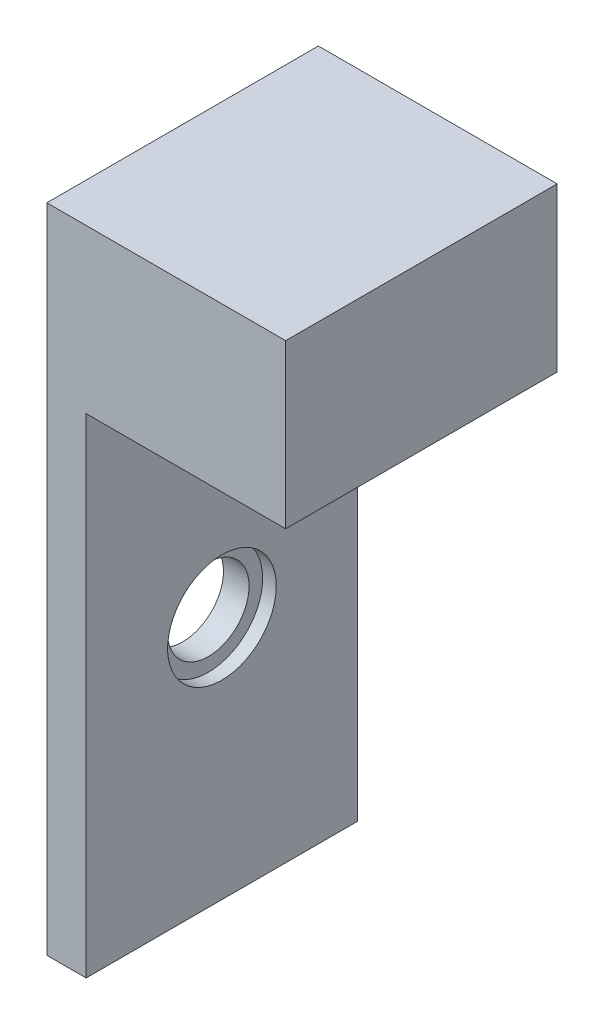
SolidWorks part; units mm, degrees
ref_plane "Plan de face" through (0, 0, 0) normal (0, 0, 1) x (1, 0, 0)
ref_plane "Plan de dessus" through (0, 0, 0) normal (0, 1, 0) x (1, 0, 0)
ref_plane "Plan de droite" through (0, 0, 0) normal (1, 0, 0) x (0, 0, -1)
sketch "Esquisse1" plane through (0, 0, 0) normal (0, 0, 1) x (1, 0, 0)
  line L1 (-11.7018, 3.0233) -> (18.2982, 3.0233)
  line L2 (-11.7018, 3.0233) -> (-11.7018, -20.9767)
  line L3 (-11.7018, -20.9767) -> (18.2982, -20.9767)
  line L4 (18.2982, 3.0233) -> (18.2982, -20.9767)
  dimension "D1" = 30
  dimension "D2" = 24
extrude "Boss.-Extru.1" add sketch "Esquisse1" along normal blind 10
sketch "Esquisse2" plane through (0, 0, 10) normal (0, 0, 1) x (1, 0, 0)
  line L0 (18.2982, 3.0233) -> (-11.7018, 3.0233) construction
  line L1 (-10.4908, 1.0233) -> (9.5092, 1.0233)
  line L2 (-10.4908, 1.0233) -> (-10.4908, -18.9767)
  line L3 (-10.4908, -18.9767) -> (9.5092, -18.9767)
  line L4 (9.5092, 1.0233) -> (9.5092, -18.9767)
  dimension "D1" = 20
  dimension "D2" = 20
  dimension "D3" = 2
extrude "Enlèv. mat.-Extru.1" cut sketch "Esquisse2" against normal blind 10
sketch "Esquisse3" plane through (0, 0, 10) normal (0, 0, 1) x (1, 0, 0)
  line L0 (18.2982, -20.9767) -> (18.2982, 3.0233) construction
  line L1 (10.9518, -20.9767) -> (18.2982, -20.9767)
  line L2 (10.9518, -20.9767) -> (10.9518, -2.9767)
  line L3 (10.9518, -2.9767) -> (18.2982, -2.9767)
  line L4 (18.2982, -20.9767) -> (18.2982, -2.9767)
  line L5 (-11.7018, -20.9767) -> (18.2982, -20.9767) construction
  line L6 (18.2982, 3.0233) -> (-11.7018, 3.0233) construction
  dimension "D1" = 0
  dimension "D2" = 6
extrude "Enlèv. mat.-Extru.2" cut sketch "Esquisse3" against normal blind 10
sketch "Esquisse5" plane through (0, 0, 10) normal (0, 0, 1) x (1, 0, 0)
  line L0 (-11.7018, -20.9767) -> (10.9518, -20.9767) construction
  line L1 (-11.7018, 3.0233) -> (9.5036, 3.0233)
  line L2 (-11.7018, 3.0233) -> (-11.7018, -20.9767)
  line L3 (-11.7018, -20.9767) -> (9.5036, -20.9767)
  line L4 (9.5036, 3.0233) -> (9.5036, -20.9767)
extrude "Enlèv. mat.-Extru.3" cut sketch "Esquisse5" against normal blind 10
sketch "Esquisse6" plane through (10.9518, 0, 0) normal (1, 0, 0) x (0, 0, -1)
  line L0 (-10, -2.9767) -> (-10, -20.9767) construction
  line L2 (0, -20.9767) -> (-10, -20.9767) construction
  circle A0 centre (-5, -11.9767) radius 2
  point P2 (-5.2168, -10.7111)
  dimension "D1" = 4
  dimension "D2" = 5
  dimension "D3" = 9
extrude "Enlèv. mat.-Extru.4" cut sketch "Esquisse6" against normal blind 0.5
sketch "Esquisse7" plane through (10.4518, 0, 0) normal (1, 0, 0) x (0, 0, -1)
  line L1 (0, -20.9767) -> (-10, -20.9767) construction
  line L3 (-10, -2.9767) -> (-10, -20.9767) construction
  circle A0 centre (-5, -11.9767) radius 1.5
  point P2 (0, 0)
  point P3 (-5.066, -11.9969)
  dimension "D1" = 3
  dimension "D2" = 9
  dimension "D3" = 5
extrude "Enlèv. mat.-Extru.5" cut sketch "Esquisse7" against normal blind 10.5
